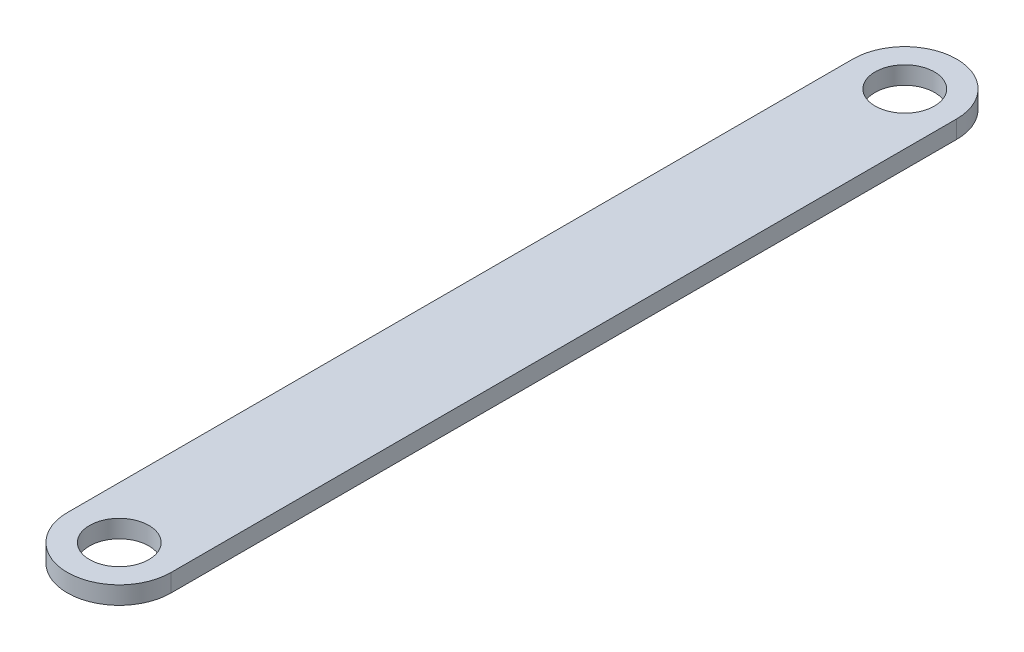
SolidWorks part; units mm, degrees
ref_plane "Front Plane" through (0, 0, 0) normal (0, 0, 1) x (1, 0, 0)
ref_plane "Top Plane" through (0, 0, 0) normal (0, 1, 0) x (1, 0, 0)
ref_plane "Right Plane" through (0, 0, 0) normal (1, 0, 0) x (0, 0, -1)
sketch "Sketch1" plane through (0, 0, 0) normal (0, 1, 0) x (1, 0, 0)
  line L0 (0, 150) -> (0, -150) construction
  line L1 (-17.5, 150) -> (17.5, 150)
  line L2 (-17.5, 150) -> (-17.5, -150)
  line L3 (-17.5, -150) -> (17.5, -150)
  line L4 (17.5, 150) -> (17.5, -150)
  line L5 (-17.5, 150) -> (17.5, -150) construction
  line L6 (-17.5, -150) -> (17.5, 150) construction
  line L7 (-17.5, 0) -> (17.5, 0) construction
  circle A0 centre (0, 132.5) radius 10
  circle A1 centre (0, 132.5) radius 17.5
  circle A2 centre (0, -132.5) radius 10
  circle A3 centre (0, -132.5) radius 17.5
  point P0 (0, 0)
  dimension "D3" = 20
  dimension "D1" = 300
  dimension "D2" = 35
extrude "Boss-Extrude1" add sketch "Sketch1" along normal blind 6 contours L2 A3 L4 A1 | A1 A0 | A3 A2
